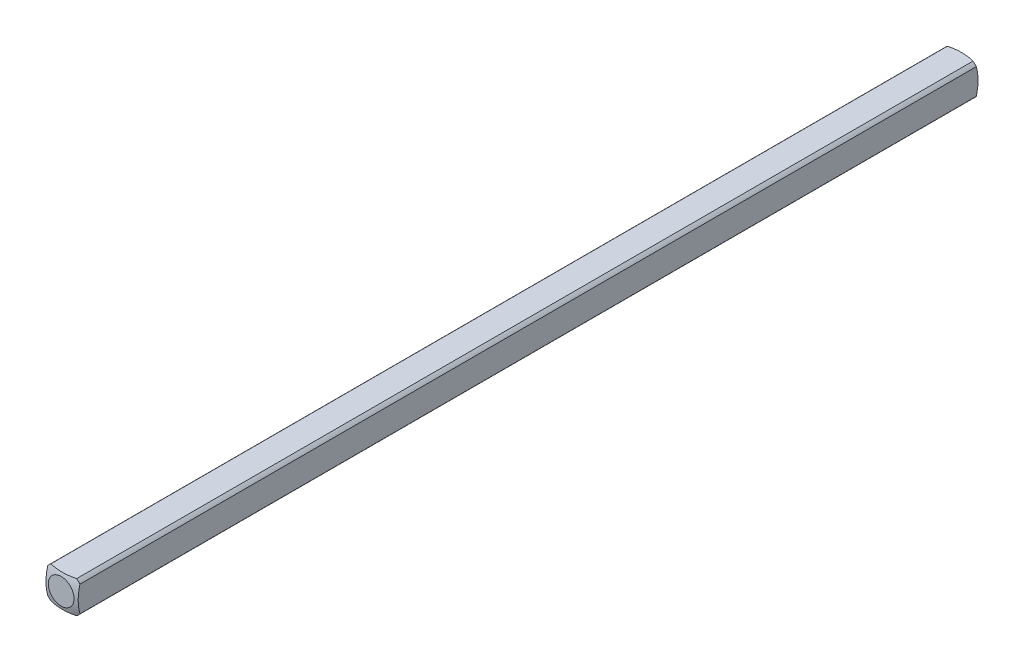
SolidWorks part; units mm, degrees
material "Custom Plastic"
ref_plane "Front Plane" through (0, 0, 0) normal (0, 0, 1) x (1, 0, 0)
ref_plane "Top Plane" through (0, 0, 0) normal (0, 1, 0) x (1, 0, 0)
ref_plane "Right Plane" through (0, 0, 0) normal (1, 0, 0) x (0, 0, -1)
sketch "Sketch1" plane through (0, 0, 0) normal (0, 0, 1) x (1, 0, 0)
  line L0 (-1.5875, -1.5875) -> (1.5875, 1.5875) construction
  line L1 (-1.5875, -1.5875) -> (1.5875, -1.5875)
  line L2 (-1.5875, -1.5875) -> (-1.5875, 1.5875)
  line L3 (-1.5875, 1.5875) -> (1.5875, 1.5875)
  line L4 (1.5875, -1.5875) -> (1.5875, 1.5875)
  dimension "D1" = 3.175
extrude "Boss-Extrude1" add sketch "Sketch1" along normal blind 44.45
sketch "Sketch2" plane through (0, 0, 0) normal (0, 0, -1) x (-1, 0, 0)
  circle A0 centre (0, 0) radius 2.032
  dimension "D1" = 4.064
extrude "Cut-Extrude1" cut sketch "Sketch2" against normal through all flip side to cut
ref_axis "Axis1" through (0, 0, 44.45) along (0, 0, -1)
sketch "Sketch3" plane through (0, 0, 0) normal (0, 1, 0) x (1, 0, 0)
  line L1 (-5.0537, -4.4027) -> (-5.0537, 5.7405)
  line L2 (-5.0537, 5.7405) -> (0, 5.7405)
  line L5 (0, -44.45) -> (0, 0) construction
  line L8 (0, 0.1609) -> (0, 5.7405)
  arc A0 (-5.0537, -4.4027) -> (0, 0.1609) centre (0, -4.9191) cw
  dimension "D1" = 5.08
revolve "Cut-Revolve1" cut sketch "Sketch3" angle 360 about axis through (0, 0, 44.45) along (0, 0, -1)
mirror "Mirror1" about plane through (0, 0, 44.45) normal (0, 0, -1) of bodies 103
